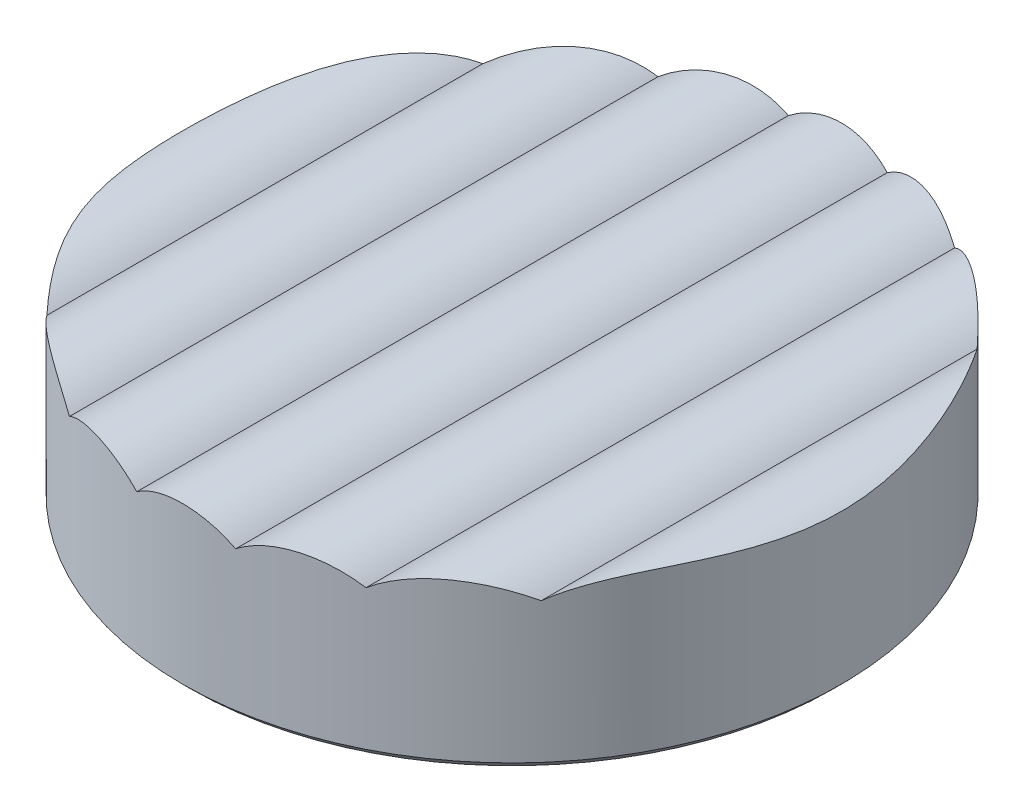
SolidWorks part; units mm, degrees
material "玻璃"
ref_plane "前视基准面" through (0, 0, 0) normal (0, 0, 1) x (1, 0, 0)
ref_plane "上视基准面" through (0, 0, 0) normal (0, 1, 0) x (1, 0, 0)
ref_plane "右视基准面" through (0, 0, 0) normal (1, 0, 0) x (0, 0, -1)
sketch "草图1" plane through (0, 0, 0) normal (0, 1, 0) x (1, 0, 0)
  circle A0 centre (0, 0) radius 4
  dimension "D1" = 8
extrude "凸台-拉伸1" add sketch "草图1" along normal blind 2
sketch "草图2" plane through (0, 0, 0) normal (0, 0, 1) x (1, 0, 0)
  line L2 (-4.4609, 1.5088) -> (-4.6829, 3.4539)
  line L3 (-4.6829, 3.4539) -> (4.9003, 2.6979)
  line L4 (4.9003, 2.6979) -> (4.2, 1.8)
  arc A2 (3, 1.8) -> (1.8, 1.8) centre (2.4, 1) ccw
  arc A3 (4.2, 1.8) -> (3, 1.8) centre (3.6, 1) ccw
  arc A10 (-3, 1.8) -> (-4.4609, 1.5088) centre (-3.6, 1) ccw
  arc A11 (-1.8, 1.8) -> (-3, 1.8) centre (-2.4, 1) ccw
  arc A12 (-0.6, 1.8) -> (-1.8, 1.8) centre (-1.2, 1) ccw
  arc A13 (0.6, 1.8) -> (-0.6, 1.8) centre (0, 1) ccw
  arc A14 (1.8, 1.8) -> (0.6, 1.8) centre (1.2, 1) ccw
extrude "切除-拉伸1" cut sketch "草图2" against normal mid plane 8
chamfer "倒角1" distance 0.1 angle 45 1 edges at (0, 0, 4)
